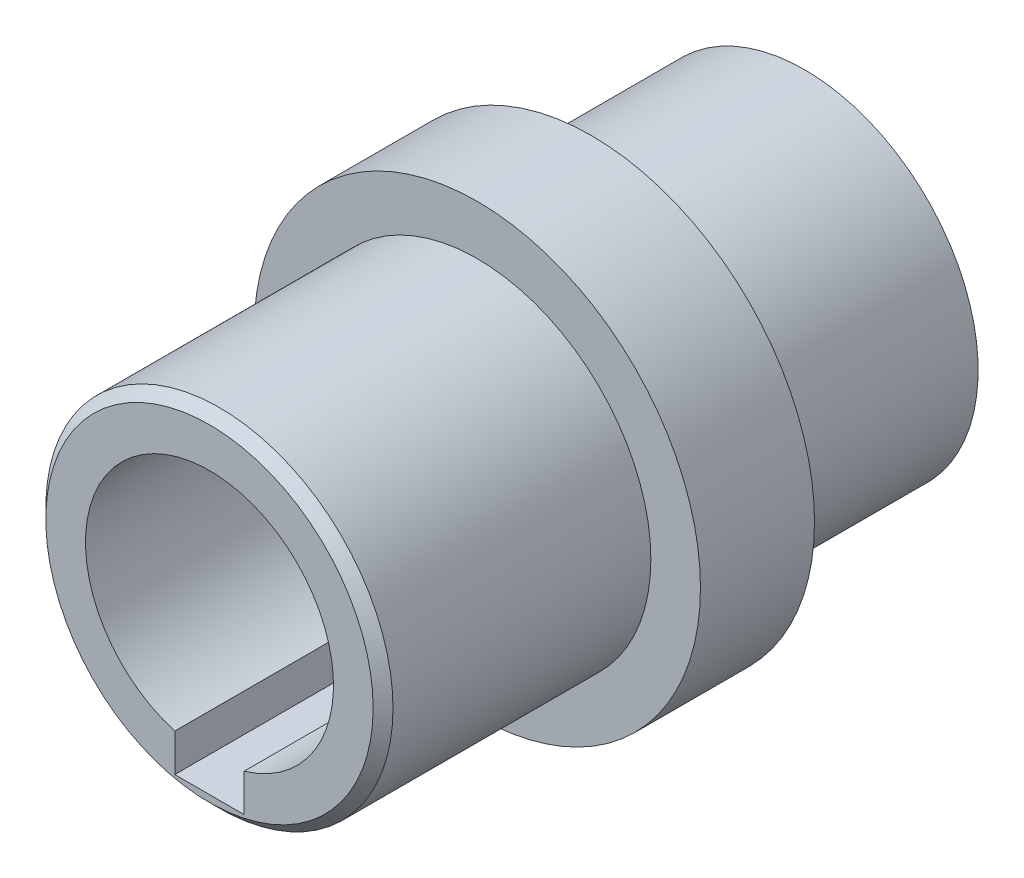
SolidWorks part; units mm, degrees
ref_plane "Plan de face" through (0, 0, 0) normal (0, 0, 1) x (1, 0, 0)
ref_plane "Plan de dessus" through (0, 0, 0) normal (0, 1, 0) x (1, 0, 0)
ref_plane "Plan de droite" through (0, 0, 0) normal (1, 0, 0) x (0, 0, -1)
sketch "Esquisse1" plane through (0, 0, 0) normal (0, 0, 1) x (1, 0, 0)
  circle A0 centre (0, 0) radius 22.5
  dimension "D1" = 45
extrude "Boss.-Extru.1" add sketch "Esquisse1" along normal blind 60
sketch "Esquisse2" plane through (0, 0, 60) normal (0, 0, 1) x (1, 0, 0)
  circle A0 centre (0, 0) radius 17.5
  dimension "D1" = 35
extrude "Enlèv. mat.-Extru.1" cut sketch "Esquisse2" against normal blind 27 flip side to cut
sketch "Esquisse3" plane through (0, 0, 0) normal (0, 0, -1) x (-1, 0, 0)
  circle A0 centre (0, 0) radius 17.5
  dimension "D1" = 35
extrude "Enlèv. mat.-Extru.2" cut sketch "Esquisse3" against normal blind 21.5 flip side to cut
sketch "Esquisse4" plane through (0, 0, 60) normal (0, 0, 1) x (1, 0, 0)
  circle A0 centre (0, 0) radius 12.5
  dimension "D1" = 25
extrude "Enlèv. mat.-Extru.3" cut sketch "Esquisse4" against normal through all
sketch "Esquisse6" plane through (0, 0, 0) normal (0, 1, 0) x (1, 0, 0)
  line L0 (0, -132.6543) -> (0, 6.7388) construction
  line L1 (-3.5, -132.6543) -> (-3.5, 6.7388)
  line L2 (3.5, -132.6543) -> (3.5, 6.7388)
  arc A0 (-3.5, -132.6543) -> (3.5, -132.6543) centre (0, -132.6543) ccw
  arc A1 (3.5, 6.7388) -> (-3.5, 6.7388) centre (0, 6.7388) ccw
  point P3 (0, -62.9577)
  dimension "D1" = 7
  dimension "D2" = 139.393
extrude "Enlèv. mat.-Extru.4" cut sketch "Esquisse6" against normal blind 15.8
chamfer "Chanfrein1" distance 1 angle 45 1 edges at (17.5, 0, 60)
